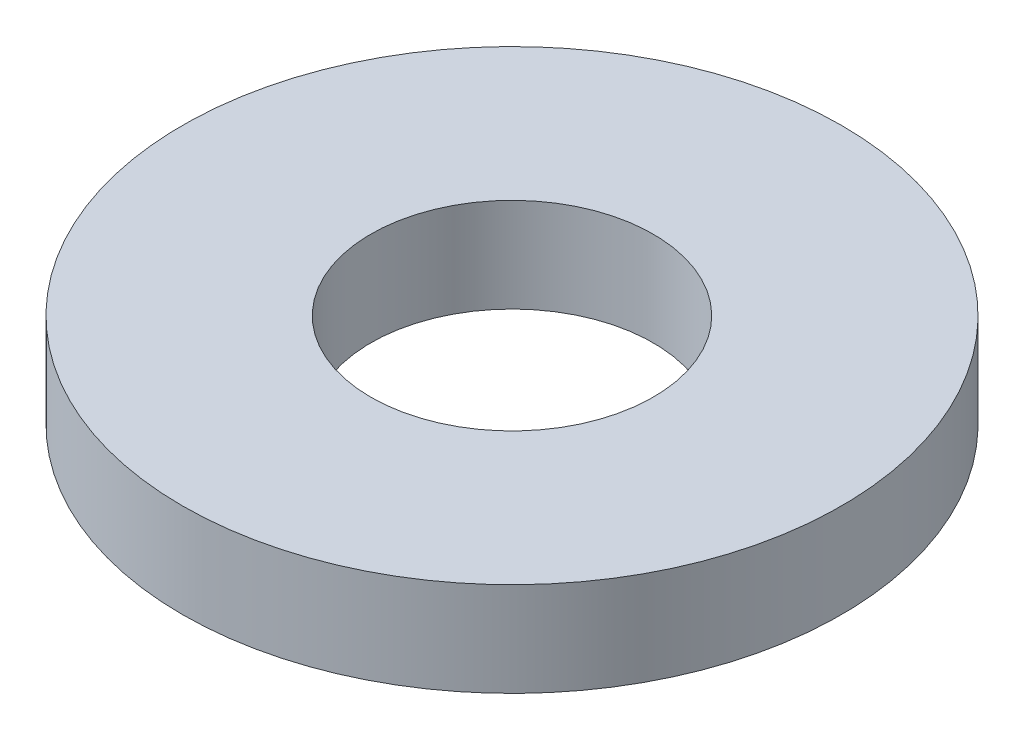
SolidWorks part; units mm, degrees
ref_plane "Front Plane" through (0, 0, 0) normal (0, 0, 1) x (1, 0, 0)
ref_plane "Top Plane" through (0, 0, 0) normal (0, 1, 0) x (1, 0, 0)
ref_plane "Right Plane" through (0, 0, 0) normal (1, 0, 0) x (0, 0, -1)
sketch "Sketch1" plane through (0, 0, 0) normal (0, 1, 0) x (1, 0, 0)
  circle A0 centre (0, 0) radius 15
  circle A1 centre (0, 0) radius 35
  point P5 (0, 0)
  point P6 (0.5808, 0)
  dimension "D1" = 30
  dimension "D2" = 70
extrude "Boss-Extrude1" add sketch "Sketch1" along normal blind 10
